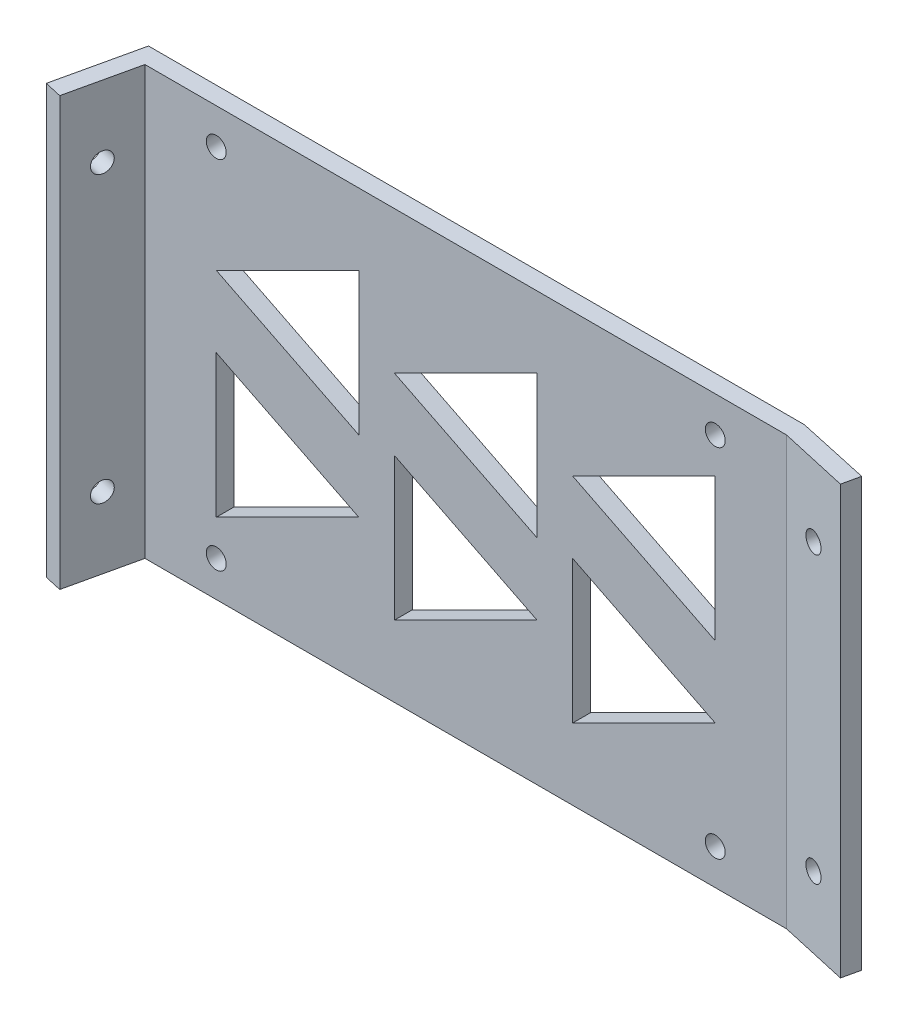
SolidWorks part; units mm, degrees
material "Copper"
ref_plane "Front Plane" through (0, 0, 0) normal (0, 0, 1) x (1, 0, 0)
ref_plane "Top Plane" through (0, 0, 0) normal (0, 1, 0) x (1, 0, 0)
ref_plane "Right Plane" through (0, 0, 0) normal (1, 0, 0) x (0, 0, -1)
sketch "Sketch1" plane through (0, 0, 0) normal (0, 0, 1) x (1, 0, 0)
  line L1 (0, 0) -> (-114.3, 0)
  line L2 (0, 0) -> (0, -76.2)
  line L3 (0, -76.2) -> (-114.3, -76.2)
  line L4 (-114.3, 0) -> (-114.3, -76.2)
  dimension "D1" = 76.2
  dimension "D2" = 114.3
extrude "Boss-Extrude1" add sketch "Sketch1" along normal blind 3.175
sketch "Sketch2" plane through (0, -76.2, 0) normal (0, -1, 0) x (1, 0, 0)
  line L0 (-114.3, 3.175) -> (-117.0878, 15.5652)
  line L1 (-117.0878, 15.5652) -> (-120.1854, 14.8683)
  line L2 (-120.1854, 14.8683) -> (-116.84, 0)
  line L3 (-116.84, 0) -> (-114.3, 0)
  line L4 (-114.3, 3.175) -> (-114.3, 0) construction
  line L9 (-114.3, 3.175) -> (-114.3, 0)
  line L10 (0, 3.175) -> (0, 0)
  line L11 (0, 3.175) -> (12.3902, 5.9628)
  line L12 (12.3902, 5.9628) -> (13.0872, 2.8652)
  line L13 (13.0872, 2.8652) -> (0, 0)
  dimension "D1" = 12.7
  dimension "D2" = 3.175
  dimension "D3" = 12.7
  dimension "D4" = 3.175
  dimension "D6" = 2.54
extrude "Boss-Extrude2" add sketch "Sketch2" against normal blind 76.2
sketch "Sketch3" plane through (-108.1124, 0, -24.3253) normal (0.9756, 0, 0.2195) x (0.2195, 0, -0.9756)
  line L0 (-40.8878, 0) -> (-40.8878, -76.2) construction
  line L1 (-28.1878, 0) -> (-40.8878, 0) construction
  circle A2 centre (-34.5378, -12.7) radius 1.778
  circle A3 centre (-34.5378, -63.5) radius 1.778
  dimension "D1" = 50.8
  dimension "D2" = 3.556
  dimension "D3" = 3.556
  dimension "D4" = 6.35
  dimension "D6" = 6.35
  dimension "D8" = 12.7
extrude "Cut-Extrude1" cut sketch "Sketch3" against normal blind 203.2
sketch "Sketch4" plane through (0, 0, 3.175) normal (0, 0, 1) x (1, 0, 0)
  line L0 (-101.6, -63.5) -> (-101.6, -38.1)
  line L1 (-101.6, -38.1) -> (-76.2, -50.8)
  line L2 (-76.2, -50.8) -> (-101.6, -63.5)
  line L3 (-101.6, -25.4) -> (-76.2, -38.1)
  line L4 (-76.2, -38.1) -> (-76.2, -12.7)
  line L5 (-76.2, -12.7) -> (-101.6, -25.4)
  line L6 (-114.3, -76.2) -> (0, -76.2) construction
  line L7 (-114.3, 0) -> (-114.3, -76.2) construction
  point P8 (0, 0)
  point P9 (0, 0)
  dimension "D1" = 25.4
  dimension "D2" = 25.4
  dimension "D3" = 12.7
  dimension "D4" = 25.4
  dimension "D5" = 25.4
  dimension "D6" = 12.7
  dimension "D7" = 12.7
  dimension "D8" = 12.7
  dimension "D9" = 12.7
  dimension "D10" = 12.7
extrude "Cut-Extrude2" cut sketch "Sketch4" against normal blind 3.175
pattern_linear "LPattern1" count 3 spacing 31.75 along (1, 0, 0) of "Cut-Extrude2"
sketch "Sketch5" plane through (0, 0, 3.175) normal (0, 0, 1) x (1, 0, 0)
  line L0 (0, 0) -> (-114.3, 0) construction
  line L1 (-114.3, 0) -> (-114.3, -76.2) construction
  line L2 (-114.3, -76.2) -> (0, -76.2) construction
  line L3 (0, -76.2) -> (0, 0) construction
  circle A0 centre (-101.6, -69.85) radius 1.778
  circle A1 centre (-12.7, -69.85) radius 1.778
  circle A2 centre (-12.7, -6.35) radius 1.778
  circle A3 centre (-101.6, -6.35) radius 1.778
  dimension "D1" = 3.556
  dimension "D2" = 3.556
  dimension "D3" = 3.556
  dimension "D4" = 3.556
  dimension "D5" = 6.35
  dimension "D6" = 12.7
  dimension "D7" = 6.35
  dimension "D8" = 12.7
  dimension "D9" = 6.35
  dimension "D10" = 6.35
  dimension "D11" = 12.7
  dimension "D12" = 12.7
extrude "Cut-Extrude3" cut sketch "Sketch5" against normal blind 3.175
sketch "Sketch6" plane through (-0.68, 0, 3.022) normal (-0.2195, 0, 0.9756) x (0.9756, 0, 0.2195)
  line L0 (13.397, 0) -> (13.397, -76.2) construction
  line L1 (13.397, -76.2) -> (0.697, -76.2) construction
  line L2 (13.397, 0) -> (0.697, 0) construction
  circle A0 centre (7.047, -63.5) radius 1.778
  circle A1 centre (7.047, -12.7) radius 1.778
  dimension "D1" = 3.556
  dimension "D2" = 3.556
  dimension "D3" = 6.35
  dimension "D4" = 12.7
  dimension "D5" = 6.35
  dimension "D6" = 12.7
extrude "Cut-Extrude4" cut sketch "Sketch6" against normal blind 3.175
